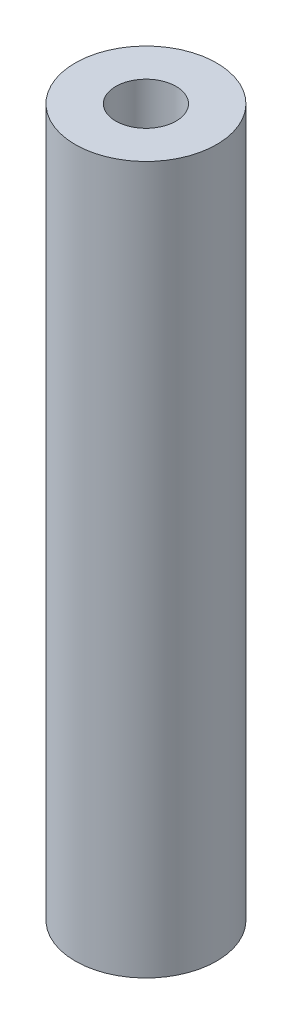
SolidWorks part; units mm, degrees
ref_plane "Front Plane" through (0, 0, 0) normal (0, 0, 1) x (1, 0, 0)
ref_plane "Top Plane" through (0, 0, 0) normal (0, 1, 0) x (1, 0, 0)
ref_plane "Right Plane" through (0, 0, 0) normal (1, 0, 0) x (0, 0, -1)
sketch "Sketch1" plane through (0, 0, 0) normal (0, 1, 0) x (1, 0, 0)
  circle A0 centre (0, 0) radius 3.175
  dimension "D1" = 6.35
extrude "Boss-Extrude1" add sketch "Sketch1" along normal blind 31.75
hole_wizard "Tap Drill for #6-32 Tap1" positions "Sketch3" profile "Sketch2" hole size "#6-32" standard "ANSI Inch" end condition through all
sketch "Sketch3" plane through (0, 31.75, 0) normal (0, 1, 0) x (1, 0, 0)
  point P0 (0, 0)
sketch "Sketch2" plane through (0, 31.75, 0) normal (1, 0, 0) x (0, 0, 1)
  line L0 (0, 0) -> (0, 31.75)
  line L1 (0, 31.75) -> (1.3525, 31.75)
  line L2 (1.3525, 31.75) -> (1.3525, 0)
  line L5 (1.3525, 0) -> (0, 0)
  line L11 (0, -6.35) -> (0, 107.95) construction
  dimension "Thru Hole Dia." = 2.7051
  dimension "Thru Hole Depth" = 31.75
